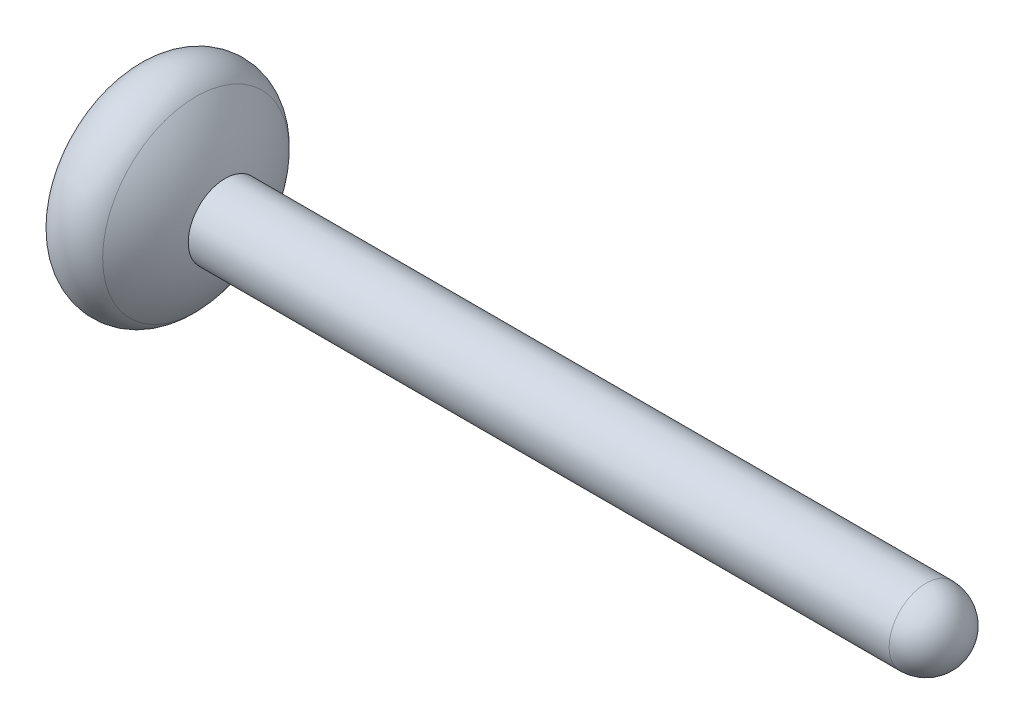
SolidWorks part; units mm, degrees
ref_plane "前视基准面" through (0, 0, 0) normal (0, 0, 1) x (1, 0, 0)
ref_plane "上视基准面" through (0, 0, 0) normal (0, 1, 0) x (1, 0, 0)
ref_plane "右视基准面" through (0, 0, 0) normal (1, 0, 0) x (0, 0, -1)
sketch "草图1" plane through (0, 0, 0) normal (0, 0, 1) x (1, 0, 0)
  line L0 (0, 0) -> (11.9, 0) construction
  line L1 (1.9, 0.5) -> (11.9, 0.5)
  line L3 (11.9, 0.5) -> (11.9, 0)
  line L5 (0, 1) -> (15, -1) construction
  line L6 (11.9, 0.5) -> (-3.1466, -1.2098) construction
  line L8 (3.2668, 0) -> (4, 0)
  line L9 (4, 0) -> (11.9, 0)
  line L10 (1.7298, 0) -> (3.2668, 0)
  line L11 (0.6, 1.0392) -> (0.9823, 1.7015)
  line L12 (1.7298, 0) -> (1.2, 0)
  arc A3 (1.0909, 0.5) -> (0.6, 1.0392) centre (0, 0) ccw
  arc A5 (1.9, 0.5) -> (0.9823, 1.7015) centre (0, 0) ccw
  arc A6 (1.0909, 0.5) -> (1.2, 0) centre (0, 0) cw
  point P6 (7.5, 0)
  dimension "D1" = 60
  dimension "D3" = 0.5
  dimension "D4" = 1.2
  dimension "D2" = 10.7
  dimension "D5" = 10
revolve "旋转2" add sketch "草图1" angle 360 about L0
fillet "圆角1" radius 0.5 2 edges at (0.9823, 0, 1.7015) (11.9, 0, 0.5)
sketch "草图2" plane through (0, 0, 0) normal (0, 0, 1) x (1, 0, 0)
  line L0 (0, 0) -> (0, 1.56)
sketch "草图3" plane through (0, 0, 0) normal (1, 0, 0) x (0, 0, -1)
  line L0 (0, 0) -> (-2.5995, 0)
  line L2 (0, 0) -> (0, 1.56) construction
sketch "草图4" plane through (0, 0, 0) normal (0, 0, 1) x (1, 0, 0)
  line L0 (0, 0) -> (12.3189, 0)
